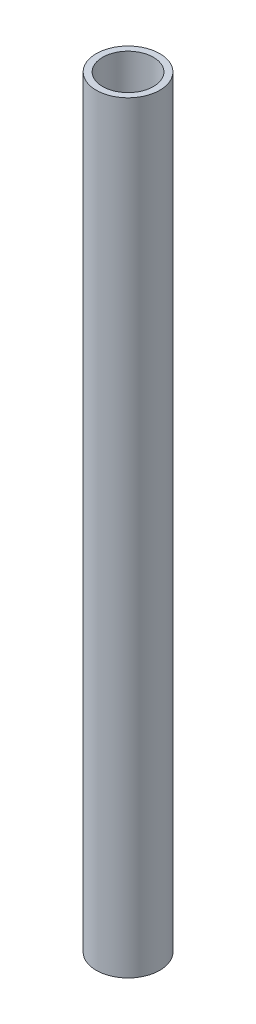
SolidWorks part; units mm, degrees
ref_plane "Спереди" through (0, 0, 0) normal (0, 0, 1) x (1, 0, 0)
ref_plane "Сверху" through (0, 0, 0) normal (0, 1, 0) x (1, 0, 0)
ref_plane "Справа" through (0, 0, 0) normal (1, 0, 0) x (0, 0, -1)
sketch "Эскиз1" plane through (0, 0, 0) normal (0, 0, 1) x (1, 0, 0)
  line L0 (0, 0) -> (0, 223.9928) construction
  line L2 (10, -67.5311) -> (12.5, -67.5311)
  line L3 (10, -67.5311) -> (10, 232.4689)
  line L4 (10, 232.4689) -> (12.5, 232.4689)
  line L5 (12.5, -67.5311) -> (12.5, 232.4689)
  dimension "D1" = 2.5
  dimension "D2" = 300
  dimension "D3" = 12.5
revolve "Повернуть1" add sketch "Эскиз1" angle 360 about L0
